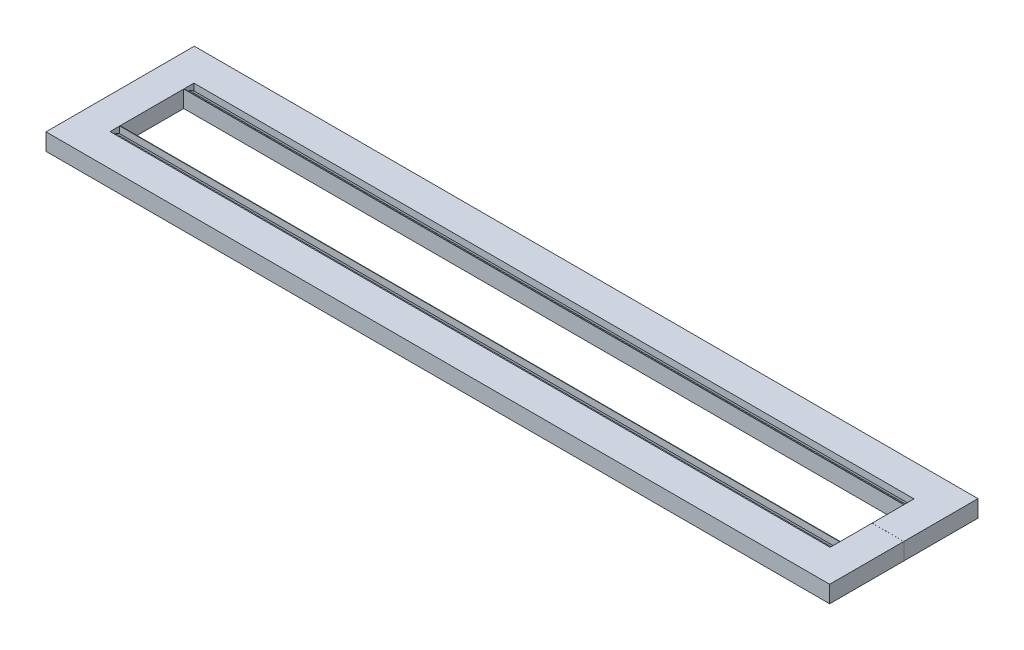
SolidWorks part; units mm, degrees
ref_plane "Front Plane" through (0, 0, 0) normal (0, 0, 1) x (1, 0, 0)
ref_plane "Top Plane" through (0, 0, 0) normal (0, 1, 0) x (1, 0, 0)
ref_plane "Right Plane" through (0, 0, 0) normal (1, 0, 0) x (0, 0, -1)
sketch "Sketch1" plane through (0, 0, 0) normal (0, 1, 0) x (1, 0, 0)
  line L0 (-199.8762, 57.4725) -> (-199.8762, 13.0225) construction
  line L1 (-434.8262, 57.4725) -> (35.0738, 57.4725)
  line L2 (16.038, 13.0225) -> (16.038, 32.0725)
  line L3 (16.038, 32.0725) -> (-415.7904, 32.0725)
  line L4 (35.0738, 57.4725) -> (35.0738, 13.0225)
  line L5 (-415.7904, 13.0225) -> (-415.7904, 32.0725)
  line L6 (-199.8762, 13.0225) -> (35.0738, 57.4725) construction
  line L7 (-434.8262, 57.4725) -> (-434.8262, 13.0225)
  line L8 (32.2526, 13.0225) -> (-199.8762, 13.0225) construction
  line L9 (-434.8262, 13.0225) -> (-415.7904, 13.0225)
  line L10 (16.038, 13.0225) -> (35.0738, 13.0225)
  line L11 (16.038, 13.0225) -> (-415.7904, 13.0225)
  line L12 (16.038, 32.0725) -> (16.038, 57.4725)
  point P0 (-199.8762, 13.0225)
  point P14 (-199.8762, 32.0725)
  dimension "D1" = 19.05
extrude "Boss-Extrude1" add sketch "Sketch1" along normal blind 10.16 contours L3 L12 L1 L7 L9 L5 | L12 L2 L10 L4 L1
sketch "Sketch2" plane through (0, 10.16, 0) normal (0, 1, 0) x (1, 0, 0)
  line L0 (15.3645, 14.5465) -> (15.3645, 57.4725)
  line L1 (-434.8262, 57.4725) -> (35.0738, 57.4725) construction
  line L2 (16.038, 13.0225) -> (16.038, 32.0725) construction
  line L3 (16.038, 13.0225) -> (16.038, 32.0725)
  line L4 (-434.8262, 57.4725) -> (35.0738, 57.4725)
  line L5 (16.038, 32.0725) -> (16.038, 57.4725)
  line L6 (35.0738, 57.4725) -> (35.0738, 13.0225) construction
  line L7 (35.0738, 57.4725) -> (35.0738, 13.0225)
sketch "Sketch3" plane through (35.0738, 0, 0) normal (1, 0, 0) x (0, 0, -1)
  line L0 (57.4725, 10.16) -> (13.0225, 10.16) construction
  line L1 (57.4725, 10.16) -> (13.0225, 10.16)
  line L4 (32.3389, 10.16) -> (32.3389, 6.1527)
  line L5 (35.2475, 7.8319) -> (32.3389, 6.1527)
  line L6 (35.2475, 7.8319) -> (38.156, 6.1527)
  line L7 (38.156, 10.16) -> (38.156, 6.1527)
  line L8 (32.3389, 10.16) -> (38.156, 10.16)
extrude "Cut-Extrude1" cut sketch "Sketch3" against normal blind 469.9 contours L7 L1 L4 L5 L6
sketch "Sketch7" plane through (35.0738, 0, 0) normal (1, 0, 0) x (0, 0, -1)
  line L0 (28.3559, 10.16) -> (28.3559, 4.4679)
  line L1 (28.3559, 10.16) -> (40.7589, 10.16)
  line L2 (28.3559, 4.4679) -> (40.7589, 4.4679)
  line L3 (40.7589, 10.16) -> (40.7589, 4.4679)
  line L4 (57.4725, 10.16) -> (13.0225, 10.16) construction
extrude "Boss-Extrude2" add sketch "Sketch7" against normal blind 19.05
sketch "Sketch8" plane through (-434.8262, 0, 0) normal (-1, 0, 0) x (0, 0, 1)
  line L0 (-57.4725, 10.16) -> (-57.4725, 0)
  line L1 (-57.4725, 10.16) -> (-12.9988, 10.16)
  line L2 (-57.4725, 0) -> (-12.9988, 0)
  line L3 (-12.9988, 10.16) -> (-12.9988, 0)
extrude "Boss-Extrude3" add sketch "Sketch8" against normal blind 19.05
ref_plane "Plane3" through (0, 0, -13.0106) normal (0, 0, 1) x (1, 0, 0)
sketch "Sketch9" plane through (0, 0, -13.0106) normal (0, 0, 1) x (1, 0, 0)
  line L0 (-430.6828, 6.1804) -> (95.5684, 6.1804) construction
mirror "Mirror1" about plane through (-415.7762, 10.16, -12.9988) normal (0, 0, 1) of bodies 105
sketch "Sketch11" plane through (0, 0, 0) normal (0, -1, 0) x (1, 0, 0)
  line L0 (-425.1563, 31.4749) -> (-425.1563, -53.6177) construction
  line L1 (-434.8262, 31.4749) -> (35.0738, 31.4749) construction
  line L2 (-199.8762, 31.4749) -> (-199.8762, -116.9894) construction
  line L3 (16.038, 6.0749) -> (-415.7762, 6.0749) construction
  line L4 (16.038, 6.0749) -> (-415.7762, 6.0749)
  line L5 (-430.6828, -13.0106) -> (95.5684, -13.0106) construction
  line L6 (-430.6828, -13.0106) -> (95.5684, -13.0106)
  line L7 (-434.8262, -57.4725) -> (35.0738, -57.4725) construction
  circle A0 centre (-425.1563, 10.2268) radius 5.7912
  circle A1 centre (-425.1563, -36.248) radius 5.7912
  circle A2 centre (25.4039, -36.248) radius 5.7912
  circle A3 centre (25.4039, 10.2268) radius 5.7912
  dimension "D1" = 21.2244
extrude "Cut-Extrude2" cut sketch "Sketch11" against normal blind 3.81 contours A0 | A2 | A3 | A1
sketch "Sketch12" plane through (0, 0, 31.4749) normal (0, 0, 1) x (1, 0, 0)
  line L0 (-243.9422, -202.7443) -> (-241.817, -197.1758)
  line L5 (-199.8762, -28.6923) -> (-199.8762, 81.4582)
